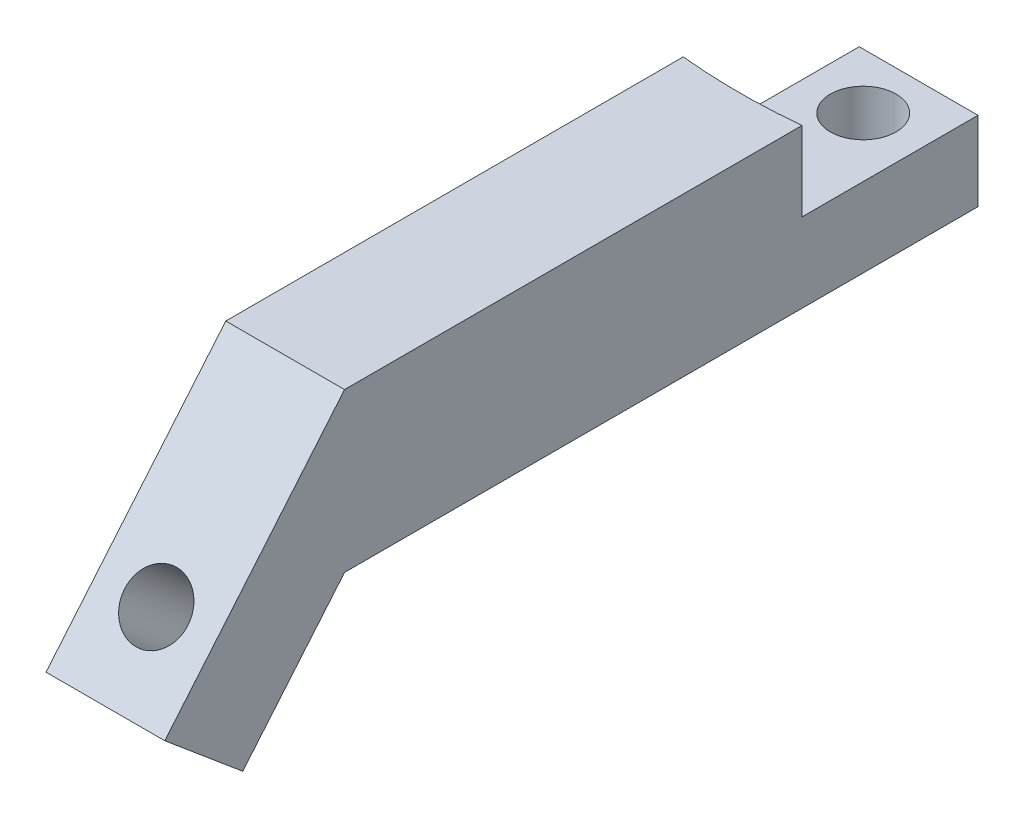
SolidWorks part; units mm, degrees
ref_plane "Спереди" through (0, 0, 0) normal (0, 0, 1) x (1, 0, 0)
ref_plane "Сверху" through (0, 0, 0) normal (0, 1, 0) x (1, 0, 0)
ref_plane "Справа" through (0, 0, 0) normal (1, 0, 0) x (0, 0, -1)
sketch "Sketch1" plane through (0, 0, 0) normal (0, 1, 0) x (1, 0, 0)
  line L0 (0, 40) -> (0, -40) construction
  line L1 (7.5, -40) -> (-7.5, -40)
  line L2 (7.5, -40) -> (7.5, 40)
  line L3 (7.5, 40) -> (-7.5, 40)
  line L4 (-7.5, -40) -> (-7.5, 40)
  line L5 (7.5, -40) -> (-7.5, 40) construction
  line L6 (7.5, 40) -> (-7.5, -40) construction
  circle A0 centre (0, 33) radius 4.15
  circle A1 centre (0, -36) radius 1.5 construction
  point P0 (0, 0)
  dimension "D1" = 8.3
  dimension "D5" = 3
  dimension "D2" = 7
  dimension "D3" = 80
  dimension "D4" = 15
  dimension "D6" = 4
extrude "Boss-Extrude1" add sketch "Sketch1" along normal blind 10
sketch "Sketch2" plane through (0, 10, 0) normal (0, 1, 0) x (1, 0, 0)
  line L0 (0, -40) -> (0, 40) construction
  line L1 (-7.5, -40) -> (7.5, -40) construction
  line L2 (7.5, 40) -> (-7.5, 40) construction
  line L3 (7.5, -40) -> (7.5, 40) construction
  line L4 (-7.5, 40) -> (-7.5, -40) construction
  line L5 (-7.5, 13.7759) -> (-7.5, 17.7759) construction
  line L6 (7.5, 17.7759) -> (7.5, 13.7759) construction
  line L7 (7.5, 17.7759) -> (7.5, -40)
  line L8 (7.5, -40) -> (-7.5, -40)
  line L9 (-7.5, -40) -> (-7.5, 17.7759)
  arc A0 (7.5, 17.7759) -> (-7.5, 17.7759) centre (0, 92.4) cw
  arc A1 (-7.5, 13.7759) -> (7.5, 13.7759) centre (0, 88.4) ccw construction
  point P16 (0, 17.4)
  dimension "D2" = 75
  dimension "D3" = 22.6
  dimension "D1" = 4
extrude "Boss-Extrude2" add sketch "Sketch2" along normal blind 10
sketch "Sketch10" plane through (7.5, 0, 0) normal (1, 0, 0) x (0, 0, -1)
  line L0 (-40, 0) -> (-52.8558, -15.3209)
  line L1 (-52.8558, -15.3209) -> (-62.7038, -7.0574)
  line L2 (-62.7038, -7.0574) -> (-40, 20)
  line L3 (-40, 0) -> (40, 0) construction
  line L6 (-40, 0) -> (-40, 20)
  dimension "D1" = 130
  dimension "D2" = 20
extrude "Boss-Extrude4" add sketch "Sketch10" against normal up to surface (15 mm away) up to face at (-7.5, 10, -5.9253)
sketch "Sketch11" plane through (0, 19.6962, 23.473) normal (0, -0.6428, -0.766) x (-1, 0, 0)
  line L0 (0, -45.7115) -> (0, -25.7115) construction
  line L1 (7.5, -45.7115) -> (-7.5, -45.7115) construction
  line L2 (7.5, -25.7115) -> (-7.5, -25.7115) construction
  circle A0 centre (0, -35.7115) radius 4
  dimension "D1" = 8
extrude "Cut-Extrude5" cut sketch "Sketch11" against normal through all
